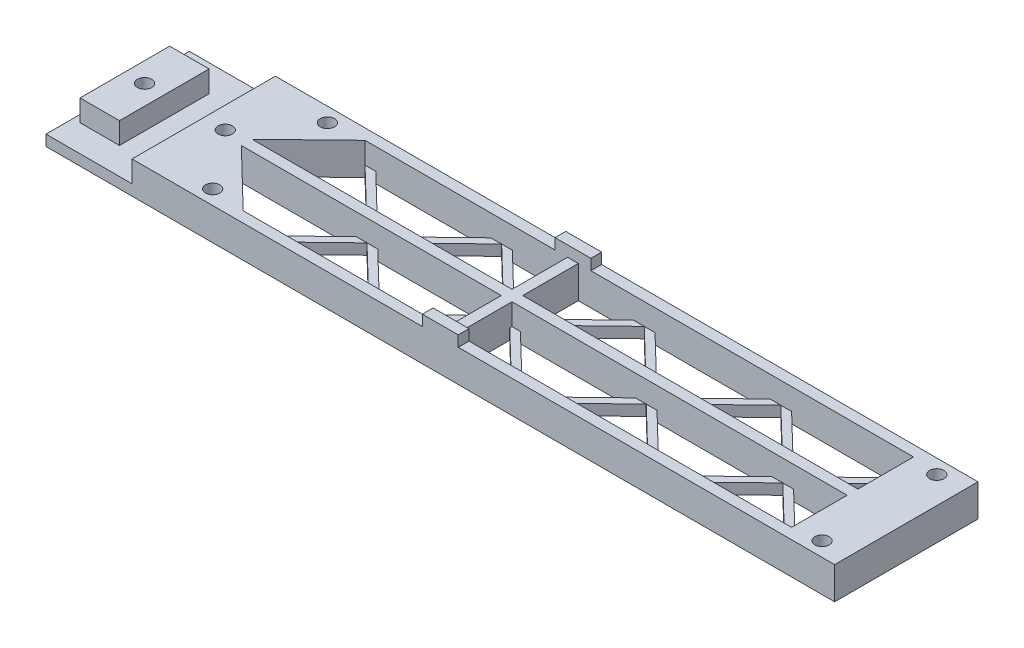
SolidWorks part; units mm, degrees
ref_plane "Front Plane" through (0, 0, 0) normal (0, 0, 1) x (1, 0, 0)
ref_plane "Top Plane" through (0, 0, 0) normal (0, 1, 0) x (1, 0, 0)
ref_plane "Right Plane" through (0, 0, 0) normal (1, 0, 0) x (0, 0, -1)
sketch "BaseSketch" plane through (0, 0, 0) normal (0, 1, 0) x (1, 0, 0)
  line L1 (110, 20) -> (-110, 20)
  line L2 (110, 20) -> (110, -20)
  line L7 (110, -20) -> (-110, -20)
  line L8 (-110, 20) -> (-110, -20)
  line L9 (110, 20) -> (-110, -20) construction
  line L10 (110, -20) -> (-110, 20) construction
  point P0 (0, 0)
  dimension "D1" = 220
  dimension "D2" = 40
extrude "Base" add sketch "BaseSketch" along normal blind 3
sketch "HolesSketch" plane through (0, 0, 0) normal (0, -1, 0) x (1, 0, 0)
  line L0 (-110, 0) -> (-102.5, 0) construction
  line L2 (-110, -20) -> (-110, 20) construction
  line L3 (-102.5, 0) -> (-80, 0) construction
  line L4 (-110, 16) -> (-67.5, 16) construction
  line L5 (-110, -16) -> (-67.5, -16) construction
  line L6 (110, -20) -> (-110, -20) construction
  line L7 (-110, 20) -> (110, 20) construction
  line L8 (110, -16) -> (102.5, -16) construction
  line L9 (110, 20) -> (110, -20) construction
  line L10 (110, 16) -> (102.5, 16) construction
  circle A0 centre (-102.5, 0) radius 2
  circle A1 centre (-80, 0) radius 2
  circle A2 centre (-67.5, 16) radius 2
  circle A3 centre (-67.5, -16) radius 2
  circle A4 centre (102.5, -16) radius 2
  circle A5 centre (102.5, 16) radius 2
  dimension "D6" = 4
  dimension "D1" = 42.5
  dimension "D2" = 4
  dimension "D3" = 4
  dimension "D4" = 7.5
  dimension "D5" = 22.5
  dimension "D7" = 7.5
extrude "Holes" cut sketch "HolesSketch" against normal through all
sketch "SupportSketch" plane through (0, 3, 0) normal (0, 1, 0) x (1, 0, 0)
  line L0 (0, 41.1208) -> (0, -41.1208) construction
  line L1 (137.2427, 0) -> (-137.2427, 0) construction
  line L2 (-47.5, 0) -> (-47.5, -50000) construction
  line L3 (110, 20) -> (-110, 20) construction
  line L4 (110, 20) -> (-110, 20) construction
  line L9 (-1.5, 0) -> (1.5, 0) construction
  line L15 (1.5, 0) -> (1.5, -50000) construction
  line L19 (-86, 0) -> (-86, -50000) construction
  line L20 (-58, 0) -> (-58, -50000) construction
  line L21 (-110, 0) -> (-102.5, 0) construction
  line L22 (-110, 20) -> (-110, -20) construction
  line L23 (1.5, 1.5) -> (1.5, -1.5) construction
  line L24 (-108, 12.5) -> (-97, 12.5)
  line L25 (-108, 12.5) -> (-108, -12.5)
  line L26 (-108, -12.5) -> (-97, -12.5)
  line L27 (-97, 12.5) -> (-97, -12.5)
  line L28 (-108, 12.5) -> (-97, -12.5) construction
  line L29 (-108, -12.5) -> (-97, 12.5) construction
  line L33 (1.5, -1.5) -> (95, -1.5)
  line L34 (1.5, -1.5) -> (1.5, -17)
  line L35 (1.5, -17) -> (95, -17)
  line L36 (95, -1.5) -> (95, -17)
  line L38 (95, 17) -> (1.5, 17)
  line L39 (95, 17) -> (95, 1.5)
  line L40 (95, 1.5) -> (1.5, 1.5)
  line L41 (1.5, 17) -> (1.5, 1.5)
  line L43 (-1.5, 0) -> (-1.5, -50000) construction
  line L44 (-1.5, -17) -> (-58, -17)
  line L48 (-47.5, -1.5) -> (-1.5, -1.5)
  line L49 (-1.5, -1.5) -> (-1.5, -17)
  line L50 (-1.5, 17) -> (-1.5, 1.5)
  line L51 (-1.5, 1.5) -> (-47.5, 1.5)
  line L55 (-58, 17) -> (-1.5, 17)
  line L63 (-110, -20) -> (110, -20) construction
  line L65 (-58, 17) -> (-74, 1.5)
  line L66 (-47.5, 1.5) -> (-74, 1.5)
  line L67 (-74, -1.5) -> (-58, -17)
  line L68 (-74, -1.5) -> (-47.5, -1.5)
  line L69 (110, -20) -> (110, 20) construction
  line L70 (110, 20) -> (110, -20)
  line L71 (110, -20) -> (-86, -20)
  line L72 (-86, -20) -> (-86, 20)
  line L73 (-86, 20) -> (110, 20)
  point P3 (0, 0)
  point P6 (0, 0)
  point P17 (0, 0)
  point P41 (1.5, 0)
  point P44 (-1.5, 0)
  dimension "D1" = 7.5
  dimension "D2" = 3
  dimension "D3" = 3
  dimension "D4" = 3
  dimension "D5" = 15
  dimension "D6" = 24
  dimension "D7" = 52
  dimension "D8" = 62.5
  dimension "D9" = 25
  dimension "D10" = 11
  dimension "D11" = 3
  dimension "D12" = 3
  dimension "D13" = 26.5
  dimension "D14" = 26.5
  dimension "D15" = 3
  dimension "D17" = 15
extrude "Support" add sketch "SupportSketch" along normal blind 6
sketch "ConnectorSketch" plane through (0, 9, 0) normal (0, 1, 0) x (1, 0, 0)
  line L0 (0, -18.5) -> (0, 18.5) construction
  line L1 (-1.5, -17) -> (-58, -17) construction
  line L2 (5, -20) -> (-5, -20)
  line L3 (5, -20) -> (5, -17)
  line L4 (5, -17) -> (-5, -17)
  line L5 (-5, -20) -> (-5, -17)
  line L6 (5, -20) -> (-5, -17) construction
  line L7 (5, -17) -> (-5, -20) construction
  line L8 (110, 20) -> (-86, 20) construction
  line L9 (5, 17) -> (-5, 17)
  line L10 (5, 17) -> (5, 20)
  line L11 (5, 20) -> (-5, 20)
  line L12 (-5, 17) -> (-5, 20)
  line L13 (5, 17) -> (-5, 20) construction
  line L14 (5, 20) -> (-5, 17) construction
  point P4 (0, 0)
  dimension "D1" = 37
  dimension "D2" = 10
extrude "Connector" add sketch "ConnectorSketch" along normal blind 3
sketch "WeightReductionSketch" plane through (0, 9, 0) normal (0, 1, 0) x (1, 0, 0)
  line L0 (-74, 1.5) -> (-58, 17)
  line L1 (-58, 17) -> (-41.9493, 1.5)
  line L2 (-1.5, 1.5) -> (-74, 1.5) construction
  line L3 (-41.9493, 1.5) -> (-74, 1.5)
  line L4 (-55, 17) -> (-38.9493, 1.5)
  line L5 (-58, 17) -> (-1.5, 17) construction
  line L6 (-38.9493, 1.5) -> (-22.8986, 17)
  line L7 (-58, 17) -> (-5, 17) construction
  line L8 (-22.8986, 17) -> (-55, 17)
  line L10 (-19.8986, 17) -> (-35.9493, 1.5)
  line L11 (-1.5, 1.5) -> (-74, 1.5) construction
  line L12 (-35.9493, 1.5) -> (-3.8478, 1.5)
  line L13 (-3.8478, 1.5) -> (-19.8986, 17)
  line L14 (-16.8986, 17) -> (-1.5, 2.1298)
  line L15 (-1.5, 17) -> (-1.5, 1.5) construction
  line L16 (-1.5, 2.1298) -> (-1.5, 17)
  line L17 (-5, 17) -> (5, 17) construction
  line L18 (-1.5, 17) -> (-16.8986, 17)
  line L19 (1.5, 2.1298) -> (16.8986, 17)
  line L20 (1.5, 17) -> (1.5, 1.5) construction
  line L21 (95, 17) -> (5, 17) construction
  line L22 (16.8986, 17) -> (1.5, 17)
  line L23 (1.5, 17) -> (-1.5, 17) construction
  line L24 (1.5, 17) -> (1.5, 2.1298)
  line L25 (3.8478, 1.5) -> (19.8986, 17)
  line L26 (95, 1.5) -> (1.5, 1.5) construction
  line L27 (19.8986, 17) -> (35.9493, 1.5)
  line L28 (95, 1.5) -> (1.5, 1.5) construction
  line L29 (35.9493, 1.5) -> (3.8478, 1.5)
  line L30 (38.9493, 1.5) -> (22.8986, 17)
  line L31 (22.8986, 17) -> (55, 17)
  line L32 (55, 17) -> (38.9493, 1.5)
  line L33 (41.9493, 1.5) -> (58, 17)
  line L34 (95, 17) -> (1.5, 17) construction
  line L37 (41.9493, 1.5) -> (74.0507, 1.5)
  line L38 (74.0507, 1.5) -> (58, 17)
  line L39 (77.0507, 1.5) -> (61, 17)
  line L40 (61, 17) -> (93.1014, 17)
  line L41 (93.1014, 17) -> (77.0507, 1.5)
  line L42 (95, 15.9364) -> (80.0507, 1.5)
  line L43 (95, 17) -> (95, 1.5) construction
  line L44 (80.0507, 1.5) -> (95, 1.5)
  line L45 (95, 1.5) -> (95, 15.9364)
  dimension "D1" = 44
  dimension "D2" = 44.091
  dimension "D3" = 3
  dimension "D4" = 3
  dimension "D5" = 44
  dimension "D6" = 3
  dimension "D7" = 3
  dimension "D8" = 44
  dimension "D9" = 3
  dimension "D10" = 3
  dimension "D11" = 44
  dimension "D12" = 3
  dimension "D13" = 3
  dimension "D14" = 44
  dimension "D15" = 3
  dimension "D16" = 3
  dimension "D17" = 44
  dimension "D18" = 3
  dimension "D19" = 3
  dimension "D20" = 44
  dimension "D21" = 3
extrude "WeightReduction" cut sketch "WeightReductionSketch" against normal through all both and the other way through all
mirror "WeightReductionMirror" about plane through (0, 0, 0) normal (0, 0, 1) of "WeightReduction"
